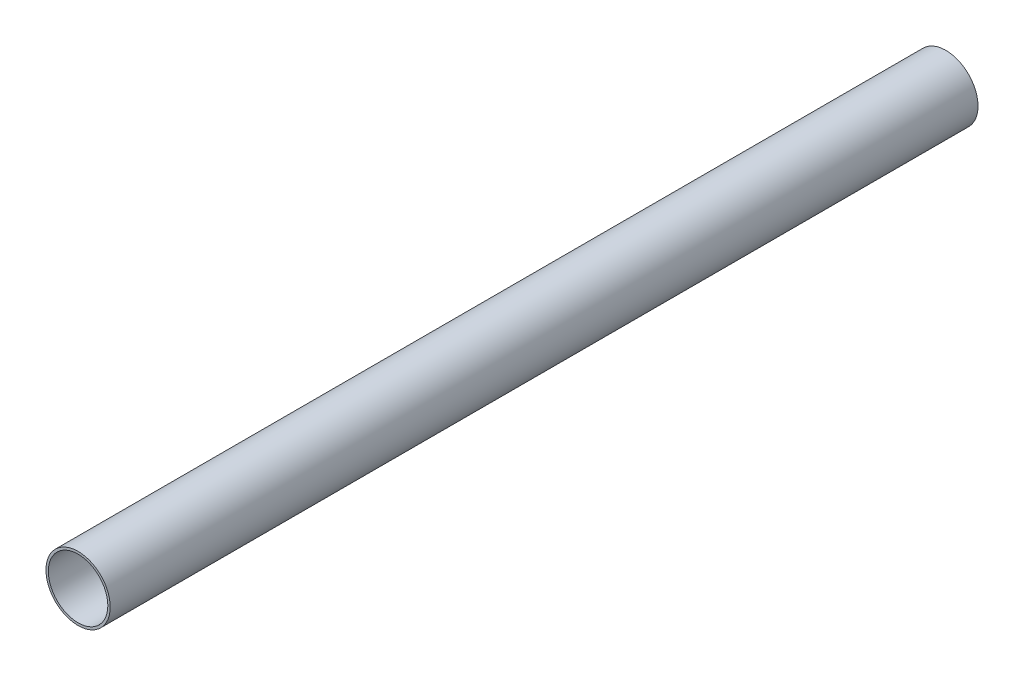
SolidWorks part; units mm, degrees
ref_plane "Front" through (0, 0, 0) normal (0, 0, 1) x (1, 0, 0)
ref_plane "Top" through (0, 0, 0) normal (0, 1, 0) x (1, 0, 0)
ref_plane "Side" through (0, 0, 0) normal (1, 0, 0) x (0, 0, -1)
sketch "PipeSketch" plane through (0, 0, 0) normal (0, 0, 1) x (1, 0, 0)
  circle A0 centre (0, 0) radius 203.2
  circle A1 centre (0, 0) radius 188.1124
  dimension "OuterDiameter" = 406.4
  dimension "InnerDiameter" = 376.2248
extrude "Extrusion" add sketch "PipeSketch" along normal blind 5486.4
sketch "FilterSketch" plane through (0, 0, 0) normal (0, 0, 1) x (1, 0, 0)
  circle A0 centre (0, 0) radius 203.2 construction
  dimension "NominalDiameter" = 406.4
